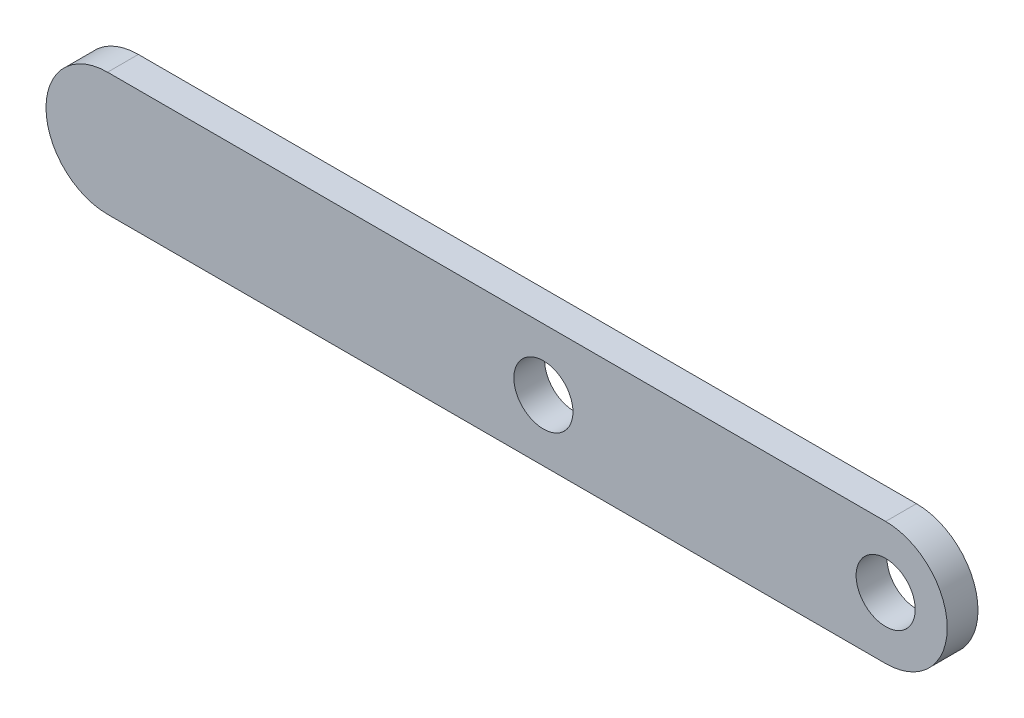
SolidWorks part; units mm, degrees
ref_plane "Front" through (0, 0, 0) normal (0, 0, 1) x (1, 0, 0)
ref_plane "Top" through (0, 0, 0) normal (0, 1, 0) x (1, 0, 0)
ref_plane "Right" through (0, 0, 0) normal (1, 0, 0) x (0, 0, -1)
sketch "Sketch1" plane through (0, 0, 0) normal (0, 0, 1) x (1, 0, 0)
  line L1 (-40.132, -6.35) -> (40.132, -6.35)
  line L2 (-40.132, -6.35) -> (-40.132, 6.35) construction
  line L3 (-40.132, 6.35) -> (40.132, 6.35)
  line L4 (40.132, -6.35) -> (40.132, 6.35) construction
  line L5 (-40.132, -6.35) -> (40.132, 6.35) construction
  line L6 (-40.132, 6.35) -> (40.132, -6.35) construction
  arc A0 (-40.132, 6.35) -> (-40.132, -6.35) centre (-40.132, 0) ccw
  arc A1 (40.132, -6.35) -> (40.132, 6.35) centre (40.132, 0) ccw
  circle A2 centre (40.132, 0) radius 3.048
  circle A3 centre (4.826, 0) radius 3.048
  point P0 (0, 0)
  dimension "D4" = 6.096
  dimension "D5" = 6.096
  dimension "D1" = 12.7
  dimension "D2" = 80.264
  dimension "D3" = 35.306
extrude "Boss-Extrude1" add sketch "Sketch1" along normal blind 3.175
